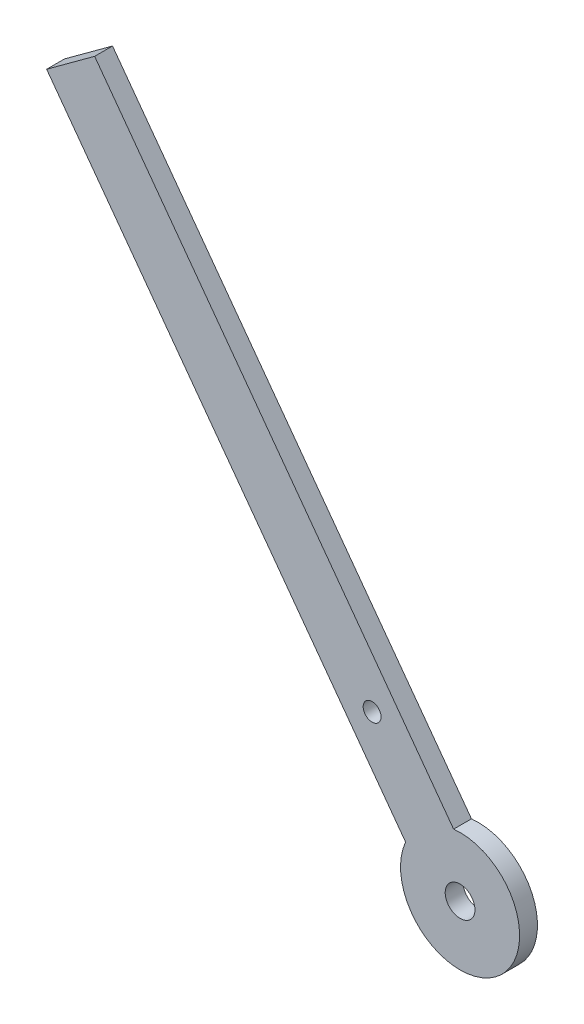
SolidWorks part; units mm, degrees
ref_plane "Front Plane" through (0, 0, 0) normal (0, 0, 1) x (1, 0, 0)
ref_plane "Top Plane" through (0, 0, 0) normal (0, 1, 0) x (1, 0, 0)
ref_plane "Right Plane" through (0, 0, 0) normal (1, 0, 0) x (0, 0, -1)
sketch "Sketch1" plane through (0, 0, 0) normal (0, 0, 1) x (1, 0, 0)
  line L13 (-65.4127, 89.2573) -> (-69.4457, 86.3017)
  line L14 (-69.4457, 86.3017) -> (-9.1521, 4.0297)
  line L15 (0, 0) -> (-65.4127, 89.2573) construction
  line L19 (-65.4127, 89.2573) -> (-61.3798, 92.2129)
  line L20 (-61.3798, 92.2129) -> (-1.0862, 9.9408)
  line L32 (-68.1739, 63.345) -> (-65.1764, 63.4689) construction
  line L34 (59.7668, 67.4254) -> (62.7642, 67.5493) construction
  circle A23 centre (0, 0) radius 2.5
  circle A24 centre (-14.7778, 20.1647) radius 1.5
  arc A25 (-9.1521, 4.0297) -> (-1.0862, 9.9408) centre (0, 0) ccw
  dimension "D1" = 5
  dimension "D2" = 102
  dimension "D6" = 3
extrude "Boss-Extrude1" add sketch "Sketch1" along normal blind 3
